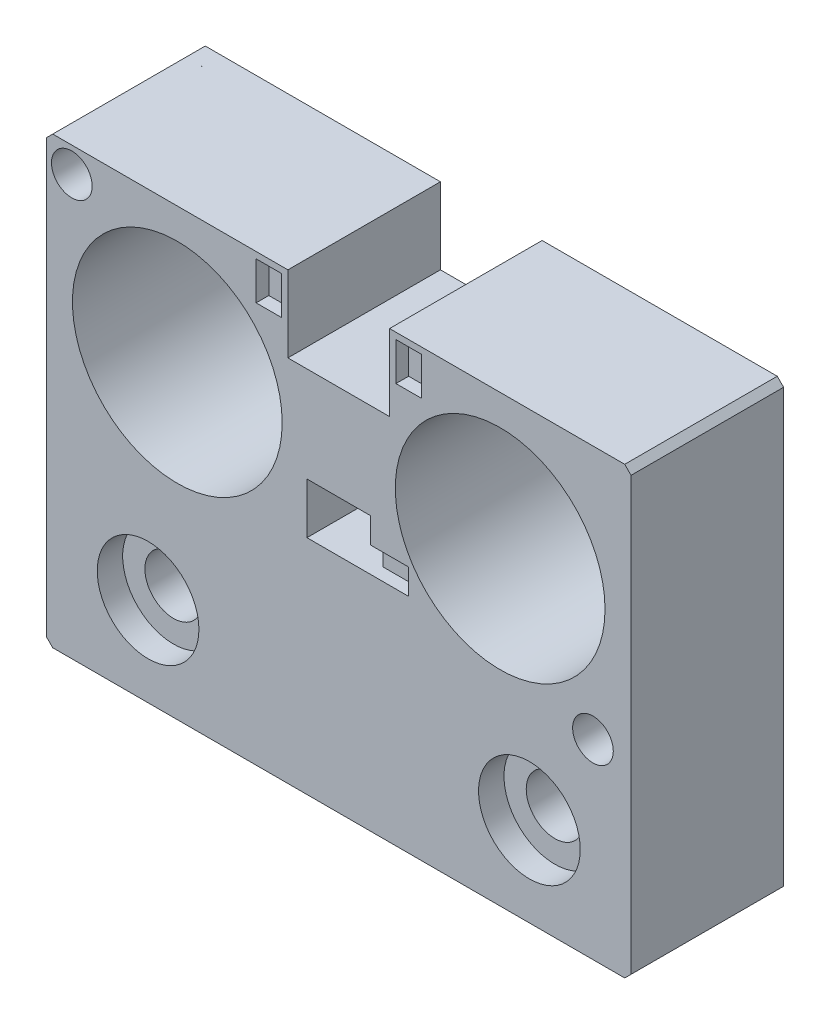
SolidWorks part; units mm, degrees
material "ABS"
ref_plane "前基準面" through (0, 0, 0) normal (0, 0, 1) x (1, 0, 0)
ref_plane "上基準面" through (0, 0, 0) normal (0, 1, 0) x (1, 0, 0)
ref_plane "右基準面" through (0, 0, 0) normal (1, 0, 0) x (0, 0, -1)
sketch "草圖1" plane through (0, 0, 0) normal (0, 0, 1) x (1, 0, 0)
  line L1 (-23, -10) -> (23, -10)
  line L2 (-23, -10) -> (-23, 10)
  line L3 (-23, 10) -> (23, 10)
  line L4 (23, -10) -> (23, 10)
  line L5 (-23, -10) -> (23, 10) construction
  line L6 (-23, 10) -> (23, -10) construction
  point P0 (0, 0)
  dimension "D1" = 46
  dimension "D2" = 20
extrude "填料-伸長1" add sketch "草圖1" along normal blind 12
sketch "草圖2" plane through (0, 0, 12) normal (0, 0, 1) x (1, 0, 0)
  line L0 (-12.7, -0.65) -> (12.7, -0.65) construction
  line L1 (23, 10) -> (-23, 10) construction
  circle A0 centre (-12.7, -0.65) radius 8.25
  circle A1 centre (12.7, -0.65) radius 8.25
  point P4 (0, -0.65)
  dimension "D1" = 25.4
  dimension "D2" = 16.5
  dimension "D3" = 10.65
extrude "除料-伸長1" cut sketch "草圖2" against normal through all
sketch "草圖3" plane through (0, 0, 12) normal (0, 0, 1) x (1, 0, 0)
  line L0 (0, 0) -> (0, 7) construction
  line L1 (23, 10) -> (-23, 10) construction
  line L2 (-4, 4) -> (4, 4)
  line L3 (-4, 4) -> (-4, 10)
  line L4 (-4, 10) -> (4, 10)
  line L5 (4, 4) -> (4, 10)
  line L6 (-4, 4) -> (4, 10) construction
  line L7 (-4, 10) -> (4, 4) construction
  dimension "D1" = 8
  dimension "D2" = 6
extrude "除料-伸長2" cut sketch "草圖3" against normal through all
sketch "草圖4" plane through (0, 0, 12) normal (0, 0, 1) x (1, 0, 0)
  line L0 (0, 0) -> (0, -5.5) construction
  line L2 (-2.5, -3.5) -> (2.5, -3.5)
  line L3 (-2.5, -3.5) -> (-2.5, -7.5)
  line L4 (-2.5, -7.5) -> (2.5, -7.5)
  line L5 (2.5, -3.5) -> (2.5, -7.5)
  line L6 (-2.5, -3.5) -> (2.5, -7.5) construction
  line L7 (-2.5, -7.5) -> (2.5, -3.5) construction
  dimension "D1" = 5
  dimension "D2" = 4
  dimension "D3" = 5.5
extrude "除料-伸長3" cut sketch "草圖4" against normal through all
sketch "草圖5" plane through (0, 0, 12) normal (0, 0, 1) x (1, 0, 0)
  line L0 (0, 0) -> (0, 8) construction
  line L1 (2.5, -7.5) -> (5.5, -7.5)
  line L2 (2.5, -7.5) -> (2.5, -5.5)
  line L3 (2.5, -5.5) -> (5.5, -5.5)
  line L4 (5.5, -7.5) -> (5.5, -5.5)
  line L5 (-5.5, 8) -> (5.5, 8) construction
  line L6 (23, 10) -> (4, 10) construction
  line L7 (-4.5, 9.5) -> (-6.5, 9.5)
  line L8 (-4.5, 9.5) -> (-4.5, 6.5)
  line L9 (-4.5, 6.5) -> (-6.5, 6.5)
  line L10 (-6.5, 9.5) -> (-6.5, 6.5)
  line L11 (-4.5, 9.5) -> (-6.5, 6.5) construction
  line L12 (-4.5, 6.5) -> (-6.5, 9.5) construction
  line L13 (6.5, 9.5) -> (4.5, 9.5)
  line L14 (6.5, 9.5) -> (6.5, 6.5)
  line L15 (6.5, 6.5) -> (4.5, 6.5)
  line L16 (4.5, 9.5) -> (4.5, 6.5)
  line L17 (6.5, 9.5) -> (4.5, 6.5) construction
  line L18 (6.5, 6.5) -> (4.5, 9.5) construction
  point P10 (0, 8)
  dimension "D1" = 2
  dimension "D2" = 3
  dimension "D3" = 2
  dimension "D4" = 3
  dimension "D5" = 11
  dimension "D6" = 0.5
extrude "除料-伸長4" cut sketch "草圖5" against normal blind 1
sketch "草圖6" plane through (0, -10, 0) normal (0, -1, 0) x (1, 0, 0)
  line L1 (-23, 12) -> (23, 12)
  line L2 (-23, 12) -> (-23, 0)
  line L3 (-23, 0) -> (23, 0)
  line L4 (23, 12) -> (23, 0)
extrude "填料-伸長2" add sketch "草圖6" along normal blind 15
sketch "草圖14" plane through (0, 0, 12) normal (0, 0, 1) x (1, 0, 0)
  line L0 (-21, 8) -> (-23, 8) construction
  line L1 (-23, 10) -> (-23, -25) construction
  line L2 (-4, 10) -> (-23, 10) construction
  circle A0 centre (-21, 8) radius 1.6
  dimension "D1" = 3.2
  dimension "D2" = 2
  dimension "D3" = 2
extrude "除料-伸長10" cut sketch "草圖14" against normal blind 46
sketch "草圖15" plane through (0, 0, 0) normal (0, 0, -1) x (-1, 0, 0)
  line L0 (-15, -18) -> (15, -18) construction
  line L1 (0, -18) -> (0, -25) construction
  line L4 (23, -25) -> (-23, -25) construction
  circle A0 centre (-15, -18) radius 2.25
  circle A1 centre (15, -18) radius 2.25
  dimension "D3" = 4.5
  dimension "D1" = 7
  dimension "D2" = 30
extrude "除料-伸長11" cut sketch "草圖15" against normal through all
sketch "Sketch1" plane through (0, 0, 12) normal (0, 0, 1) x (1, 0, 0)
  line L0 (23, 10) -> (23, -13) construction
  line L1 (23, -25) -> (23, 10) construction
  line L3 (20, -10) -> (20, -13) construction
  line L4 (20, -13) -> (23, -13) construction
  circle A0 centre (20, -10) radius 1.6
  dimension "D2" = 3.2
  dimension "D4" = 3
  dimension "D1" = 23
  dimension "D3" = 3
extrude "Cut-Extrude1" cut sketch "Sketch1" against normal through all
sketch "Sketch2" plane through (0, 0, 12) normal (0, 0, 1) x (1, 0, 0)
  circle A0 centre (-15, -18) radius 4
  circle A1 centre (15, -18) radius 4
  dimension "8" = 8
  dimension "D2" = 8
extrude "Cut-Extrude2" cut sketch "Sketch2" against normal blind 2
chamfer "Chamfer1" distance 0.5 angle 45 2 edges at (-23, 10, 6) (23, 10, 6)
chamfer "Chamfer2" distance 0.5 angle 45 2 edges at (-23, -25, 6) (23, -25, 6)
